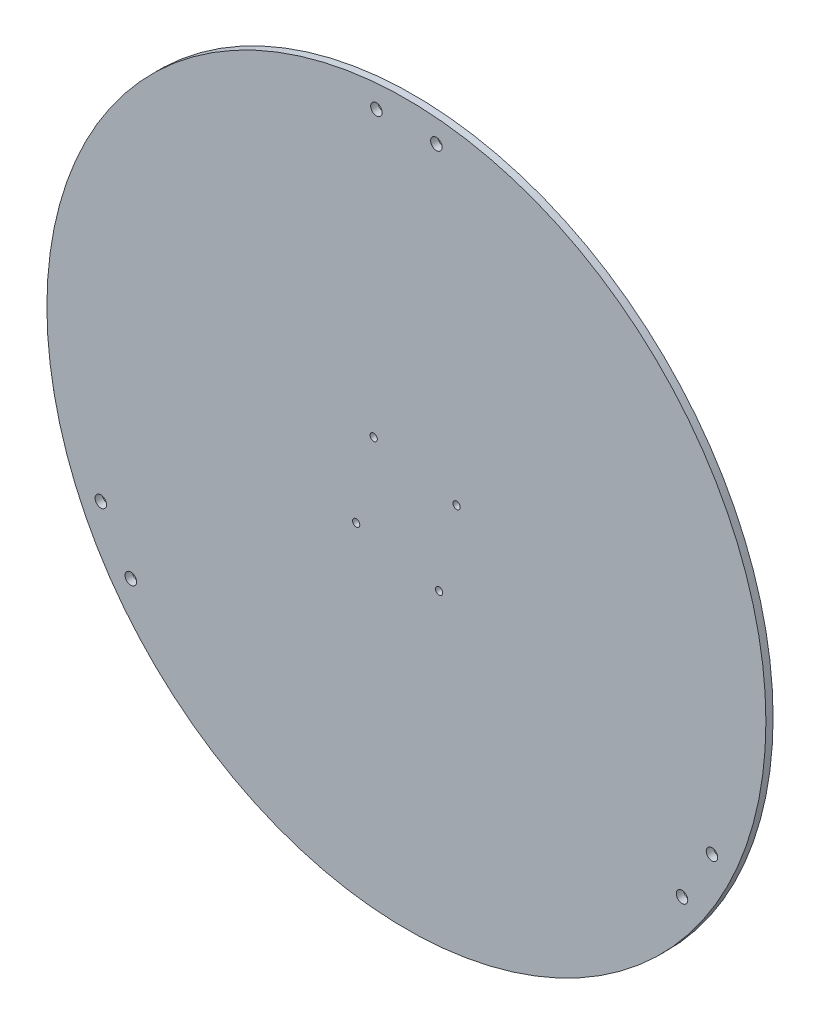
SolidWorks part; units mm, degrees
ref_plane "Front Plane" through (0, 0, 0) normal (0, 0, 1) x (1, 0, 0)
ref_plane "Top Plane" through (0, 0, 0) normal (0, 1, 0) x (1, 0, 0)
ref_plane "Right Plane" through (0, 0, 0) normal (1, 0, 0) x (0, 0, -1)
sketch "Sketch1" plane through (0, 0, 0) normal (0, 0, 1) x (1, 0, 0)
  line L0 (0, 0) -> (0, 140) construction
  line L1 (0, 140) -> (0, 150) construction
  line L2 (-12.5, 140) -> (12.5, 140) construction
  circle A0 centre (0, 0) radius 150
  circle A1 centre (12.5, 140) radius 2.4
  circle A2 centre (-12.5, 140) radius 2.4
  circle A3 centre (127.4936, -59.1747) radius 2.4
  circle A4 centre (114.9936, -80.8253) radius 2.4
  circle A5 centre (-114.9936, -80.8253) radius 2.4
  circle A6 centre (-127.4936, -59.1747) radius 2.4
  point P9 (0, 140)
  point P21 (0, 0)
  dimension "D1" = 300
  dimension "D2" = 3
  dimension "D4" = 4.8
  dimension "D3" = 25
  dimension "D5" = 140
extrude "Boss-Extrude2" add sketch "Sketch1" along normal blind 3
sketch "Sketch2" plane through (0, 0, 0) normal (0, 0, -1) x (-1, 0, 0)
  circle A13 centre (-13.6439, -20.9486) radius 3.2 construction
  circle A14 centre (20.9486, -13.6439) radius 3.2 construction
  circle A15 centre (13.6439, 20.9486) radius 3.2 construction
  circle A16 centre (-20.9486, 13.6439) radius 3.2 construction
  circle A17 centre (-13.6439, -20.9486) radius 3.2
  circle A18 centre (20.9486, -13.6439) radius 3.2
  circle A19 centre (13.6439, 20.9486) radius 3.2
  circle A20 centre (-20.9486, 13.6439) radius 3.2
  point P12 (0, 0)
hole_wizard "Ø3.0mm Dowel Hole2" positions "Sketch8" profile "Sketch9" hole size "Ø3.0" standard "ANSI Metric" end condition through all
sketch "Sketch8" plane through (0, 0, 0) normal (0, 0, -1) x (-1, 0, 0)
  point P0 (-20.9486, 13.6439)
  point P3 (13.6439, 20.9486)
  point P6 (20.9486, -13.6439)
  point P9 (-13.6439, -20.9486)
sketch "Sketch9" plane through (20.9486, 13.6439, 0) normal (1, 0, 0) x (0, 1, 0)
  line L0 (0, 0) -> (0, 3)
  line L1 (0, 3) -> (1.5, 3)
  line L2 (1.5, 3) -> (1.5, 0.025)
  line L3 (1.5, 0.025) -> (1.525, 0)
  line L5 (1.525, 0) -> (0, 0)
  line L6 (-1.5, 0.025) -> (-1.525, 0) construction
  line L11 (0, -6.35) -> (0, 107.95) construction
  dimension "Thru Hole Dia." = 3
  dimension "Thru Hole Depth" = 3
  dimension "Near C'Sink Dia." = 3.05
  dimension "Near C'Sink Angle" = 90
